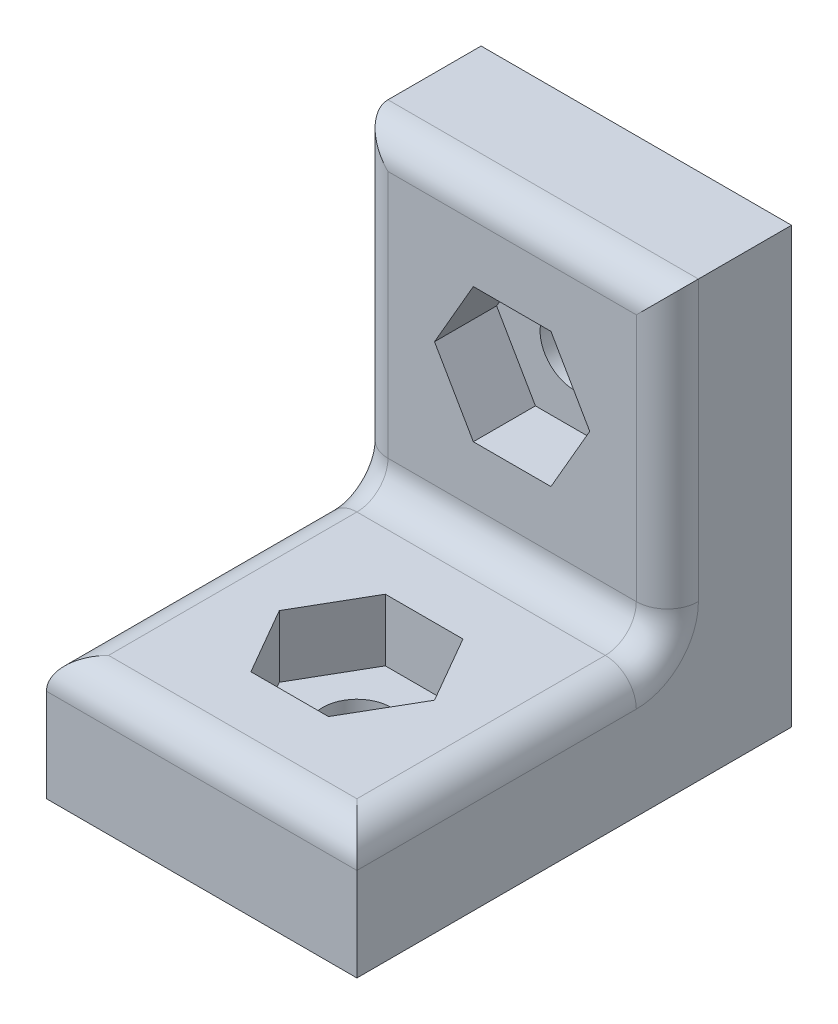
SolidWorks part; units mm, degrees
ref_plane "Plan de face" through (0, 0, 0) normal (0, 0, 1) x (1, 0, 0)
ref_plane "Plan de dessus" through (0, 0, 0) normal (0, 1, 0) x (1, 0, 0)
ref_plane "Plan de droite" through (0, 0, 0) normal (1, 0, 0) x (0, 0, -1)
sketch "Esquisse1" plane through (0, 0, 0) normal (0, 0, 1) x (1, 0, 0)
  line L1 (-5, 14) -> (5, 14)
  line L2 (-5, 14) -> (-5, 0)
  line L3 (-5, 0) -> (5, 0)
  line L4 (5, 14) -> (5, 0)
  dimension "D1" = 10
  dimension "D2" = 14
  dimension "D3" = 5
extrude "Boss.-Extru.1" add sketch "Esquisse1" along normal blind 4
sketch "Esquisse2" plane through (0, 0, 4) normal (0, 0, 1) x (1, 0, 0)
  line L0 (5, 0) -> (5, 14) construction
  line L1 (-5, 0) -> (5, 0)
  line L2 (-5, 0) -> (-5, 4)
  line L3 (-5, 4) -> (5, 4)
  line L4 (5, 0) -> (5, 4)
  dimension "D1" = 4
extrude "Boss.-Extru.2" add sketch "Esquisse2" along normal blind 10
sketch "Esquisse3" plane through (0, 0, 4) normal (0, 0, 1) x (1, 0, 0)
  line L0 (5, 14) -> (-5, 14) construction
  line L1 (-5, 14) -> (-5, 4) construction
  circle A0 centre (0, 9) radius 1.1
  point P2 (0, 14)
  point P3 (-5, 9)
  dimension "D1" = 2.2
extrude "Enlèv. mat.-Extru.1" cut sketch "Esquisse3" against normal through all
fillet "Congé1" radius 1 7 edges at (0, 4, 4) (5, 9, 4) (-5, 9, 4) (0, 14, 4) (0, 4, 14) (5, 4, 9) (-5, 4, 9)
sketch "Esquisse4" plane through (0, 4, 0) normal (0, 1, 0) x (1, 0, 0)
  line L0 (5, -14) -> (-5, -14) construction
  line L1 (-5, -14) -> (-5, -4) construction
  circle A0 centre (0, -9) radius 1.1
  point P0 (0, -14)
  point P1 (-5, -9)
  dimension "D1" = 2.2
extrude "Enlèv. mat.-Extru.2" cut sketch "Esquisse4" against normal through all
sketch "Esquisse5" plane through (0, 0, 4) normal (0, 0, 1) x (1, 0, 0)
  line L0 (5, 14) -> (-5, 14) construction
  line L1 (1.25, 6.8349) -> (2.5, 9)
  line L2 (2.5, 9) -> (1.25, 11.1651)
  line L3 (1.25, 11.1651) -> (-1.25, 11.1651)
  line L4 (-1.25, 11.1651) -> (-2.5, 9)
  line L5 (-2.5, 9) -> (-1.25, 6.8349)
  line L6 (-1.25, 6.8349) -> (1.25, 6.8349)
  circle A1 centre (0, 9) radius 2.1651 construction
  dimension "D1" = 2.5
extrude "Enlèv. mat.-Extru.3" cut sketch "Esquisse5" against normal blind 2
sketch "Esquisse6" plane through (0, 4, 0) normal (0, 1, 0) x (1, 0, 0)
  line L0 (4, -5) -> (-4, -5) construction
  line L1 (2.5, -9) -> (1.25, -6.8349)
  line L2 (1.25, -6.8349) -> (-1.25, -6.8349)
  line L3 (-1.25, -6.8349) -> (-2.5, -9)
  line L4 (-2.5, -9) -> (-1.25, -11.1651)
  line L5 (-1.25, -11.1651) -> (1.25, -11.1651)
  line L6 (1.25, -11.1651) -> (2.5, -9)
  circle A1 centre (0, -9) radius 2.1651 construction
  dimension "D1" = 2.5
extrude "Enlèv. mat.-Extru.4" cut sketch "Esquisse6" against normal blind 2
